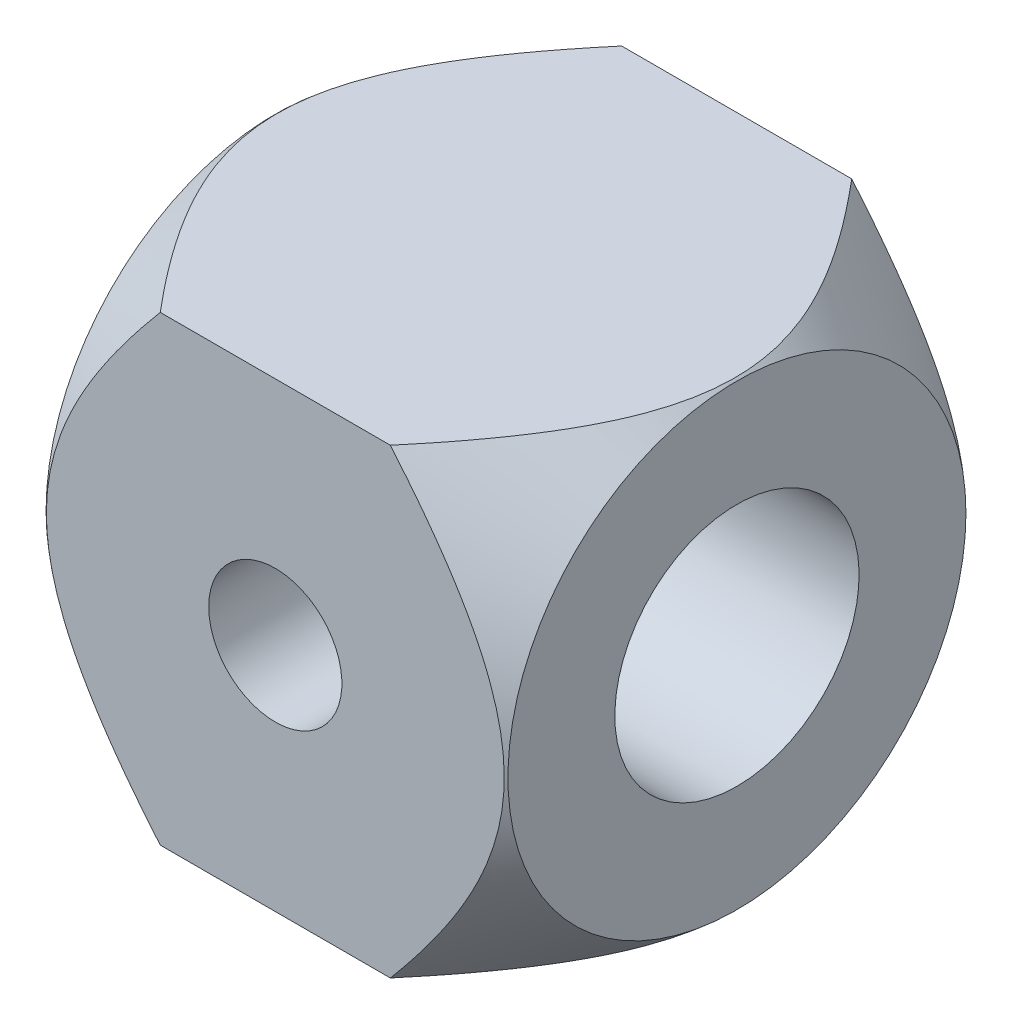
SolidWorks part; units mm, degrees
material "Brass"
ref_plane "Front Plane" through (0, 0, 0) normal (0, 0, 1) x (1, 0, 0)
ref_plane "Top Plane" through (0, 0, 0) normal (0, 1, 0) x (1, 0, 0)
ref_plane "Right Plane" through (0, 0, 0) normal (1, 0, 0) x (0, 0, -1)
sketch "Sketch3" plane through (0, 0, 0) normal (0, 0, 1) x (1, 0, 0)
  line L1 (3.4582, 3.4544) -> (-3.4582, 3.4544)
  line L2 (3.4582, 3.4544) -> (3.4582, -3.4544)
  line L3 (3.4582, -3.4544) -> (-3.4582, -3.4544)
  line L4 (-3.4582, 3.4544) -> (-3.4582, -3.4544)
  line L5 (3.4582, 3.4544) -> (-3.4582, -3.4544) construction
  line L6 (3.4582, -3.4544) -> (-3.4582, 3.4544) construction
  point P0 (0, 0)
  dimension "D1" = 6.9164
  dimension "D2" = 6.9088
extrude "Boss-Extrude2" add sketch "Sketch3" along normal mid plane 6.9088
sketch "Sketch4" plane through (0, 0, 0) normal (0, 0, 1) x (1, 0, 0)
  line L0 (3.4582, 0) -> (3.4582, 3.429)
  line L1 (3.4582, -3.4544) -> (3.4582, 3.4544) construction
  line L2 (3.4582, 3.429) -> (0.8654, 5.6046)
  line L3 (0.8654, 5.6046) -> (3.8808, 5.6046)
  line L4 (3.8808, 5.6046) -> (3.8808, 0)
  line L5 (3.8808, 0) -> (3.4582, 0)
  line L6 (0, 3.4544) -> (0, -3.4544) construction
  line L7 (3.4582, 3.4544) -> (-3.4582, 3.4544) construction
  line L8 (-3.4582, -3.4544) -> (3.4582, -3.4544) construction
  line L9 (-3.8808, 0) -> (-3.4582, 0)
  line L10 (-3.4582, 0) -> (-3.4582, 3.429)
  line L11 (-3.8808, 5.6046) -> (-3.8808, 0)
  line L12 (-0.8654, 5.6046) -> (-3.8808, 5.6046)
  line L13 (-3.4582, 3.429) -> (-0.8654, 5.6046)
  dimension "D1" = 3.429
  dimension "D2" = 130
revolve "Cut-Revolve2" cut sketch "Sketch4" angle 360 about L5
sketch "Sketch6" plane through (-3.4582, 0, 0) normal (-1, 0, 0) x (0, 0, 1)
  circle A0 centre (0, 0) radius 1.8288
  dimension "D1" = 3.6576
extrude "Cut-Extrude1" cut sketch "Sketch6" against normal blind 9.4488
sketch "Sketch7" plane through (0, 0, -3.4544) normal (0, 0, -1) x (-1, 0, 0)
  circle A0 centre (0, 0) radius 0.9969
  dimension "D1" = 1.9939
extrude "Cut-Extrude2" cut sketch "Sketch7" against normal blind 9.4488
